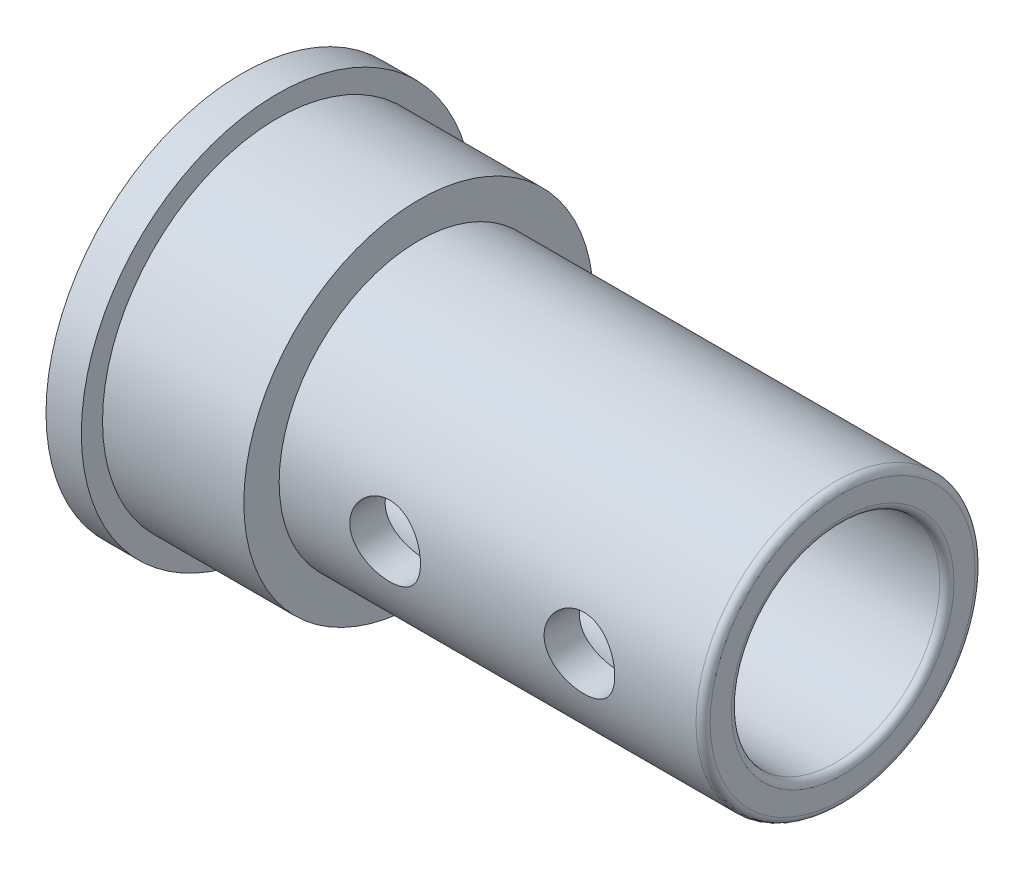
SolidWorks part; units mm, degrees
ref_plane "Plan de face" through (0, 0, 0) normal (0, 0, 1) x (1, 0, 0)
ref_plane "Plan de dessus" through (0, 0, 0) normal (0, 1, 0) x (1, 0, 0)
ref_plane "Plan de droite" through (0, 0, 0) normal (1, 0, 0) x (0, 0, -1)
sketch "Esquisse1" plane through (0, 0, 0) normal (0, 0, 1) x (1, 0, 0)
  line L0 (-11.3006, 0) -> (9.5407, 0) construction
  line L1 (0, 4.05) -> (0, 5.55)
  line L2 (0, 5.55) -> (1, 5.55)
  line L4 (5, 3.95) -> (16.8, 3.95)
  line L5 (17, 3.75) -> (17, 3.15)
  line L6 (16.8, 2.95) -> (1, 2.95)
  line L7 (1, 2.95) -> (1, 4.05)
  line L8 (1, 4.05) -> (0, 4.05)
  line L10 (1, 5.55) -> (1, 4.95)
  line L11 (1, 4.95) -> (5, 4.95)
  line L12 (5, 4.95) -> (5, 3.95)
  arc A2 (16.8, 3.95) -> (17, 3.75) centre (16.8, 3.75) cw
  arc A3 (16.8, 2.95) -> (17, 3.15) centre (16.8, 3.15) ccw
  point P19 (17, 3.95)
  point P22 (17, 2.95)
  dimension "D9" = 12
  dimension "D10" = 0.2
  dimension "D11" = 0.2
  dimension "D1" = 8.1
  dimension "D2" = 7.9
  dimension "D3" = 1
  dimension "D4" = 1.5
  dimension "D5" = 1
  dimension "D7" = 9.9
  dimension "D8" = 4
revolve "Révolution1" add sketch "Esquisse1" angle 360 about L0
hole_wizard "Dégagement M21" positions "Esquisse3" profile "Esquisse4" hole size "M2" standard "ISO"
sketch "Esquisse3" plane through (0, 0, 0) normal (0, 0, 1) x (1, 0, 0)
  point P0 (8, 0)
  point P4 (13.5, 0)
  point P7 (0, 0)
  dimension "D1" = 8
  dimension "D2" = 5.5
sketch "Esquisse4" plane through (8, 0, 0) normal (1, 0, 0) x (0, 1, 0)
  line L0 (0, 0) -> (0, 5.55)
  line L1 (0, 5.55) -> (1, 5.55)
  line L2 (1, 5.55) -> (1, 0)
  line L5 (1, 0) -> (0, 0)
  line L11 (0, -6.35) -> (0, 107.95) construction
  dimension "Diamètre du perçage jusqu'au prochain" = 2
  dimension "Profondeur du perçage jusqu'au prochain" = 5.55
